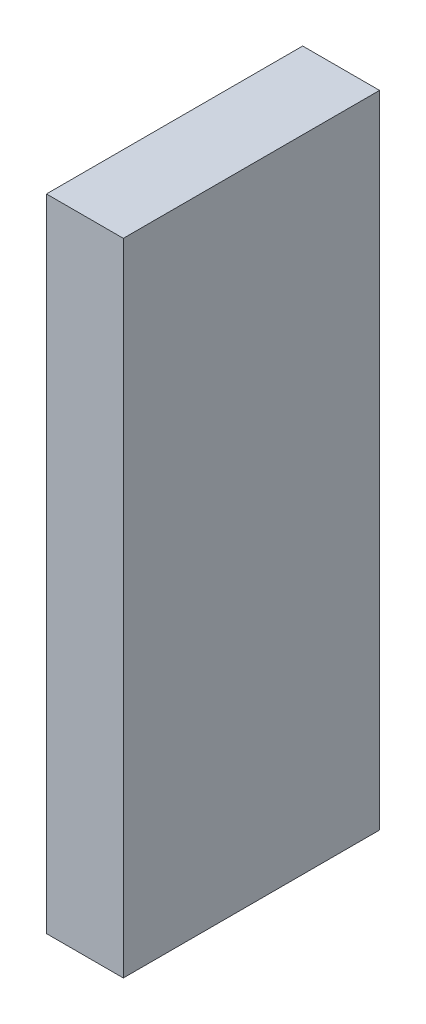
SolidWorks part; units mm, degrees
ref_plane "Front Plane" through (0, 0, 0) normal (0, 0, 1) x (1, 0, 0)
ref_plane "Top Plane" through (0, 0, 0) normal (0, 1, 0) x (1, 0, 0)
ref_plane "Right Plane" through (0, 0, 0) normal (1, 0, 0) x (0, 0, -1)
sketch "Sketch1" plane through (0, 0, 0) normal (0, 1, 0) x (1, 0, 0)
  line L1 (-6.6297, -56.1884) -> (-9.6297, -56.1884)
  line L2 (-6.6297, -56.1884) -> (-6.6297, -66.1884)
  line L3 (-6.6297, -66.1884) -> (-9.6297, -66.1884)
  line L4 (-9.6297, -56.1884) -> (-9.6297, -66.1884)
  line L12 (-12.6297, -81.1884) -> (-45.8297, -81.1884)
  line L13 (-12.6297, -56.1884) -> (-12.6297, -81.1884)
  line L14 (10.7703, -56.1884) -> (-12.6297, -56.1884)
  line L15 (10.7703, 61.3116) -> (10.7703, -56.1884)
  line L16 (45.7703, 61.3116) -> (10.7703, 61.3116)
  line L17 (45.7703, -98.6884) -> (45.7703, 61.3116)
  line L18 (-104.2297, -98.6884) -> (45.7703, -98.6884)
  line L19 (-104.2297, 61.3116) -> (-104.2297, -98.6884)
  line L20 (-69.2297, 61.3116) -> (-104.2297, 61.3116)
  line L21 (-69.2297, -56.1884) -> (-69.2297, 61.3116)
  line L22 (-45.8297, -56.1884) -> (-69.2297, -56.1884)
  line L23 (-45.8297, -81.1884) -> (-45.8297, -56.1884)
  line L24 (-12.6297, -81.1884) -> (-45.8297, -81.1884)
  line L25 (-12.6297, -56.1884) -> (-12.6297, -81.1884)
  line L26 (10.7703, -56.1884) -> (-12.6297, -56.1884)
  line L27 (10.7703, 61.3116) -> (10.7703, -56.1884)
  line L28 (45.7703, 61.3116) -> (10.7703, 61.3116)
  line L29 (45.7703, -98.6884) -> (45.7703, 61.3116)
  line L30 (-104.2297, -98.6884) -> (45.7703, -98.6884)
  line L31 (-104.2297, 61.3116) -> (-104.2297, -98.6884)
  line L32 (-69.2297, 61.3116) -> (-104.2297, 61.3116)
  line L33 (-69.2297, -56.1884) -> (-69.2297, 61.3116)
  line L34 (-45.8297, -56.1884) -> (-69.2297, -56.1884)
  line L35 (-45.8297, -81.1884) -> (-45.8297, -56.1884)
  dimension "D2" = 10
  dimension "D3" = 3
  dimension "D4" = 3
  dimension "D1" = 0
extrude "Boss-Extrude1" add sketch "Sketch1" along normal blind 25 contours L1 L4 L3 L2
